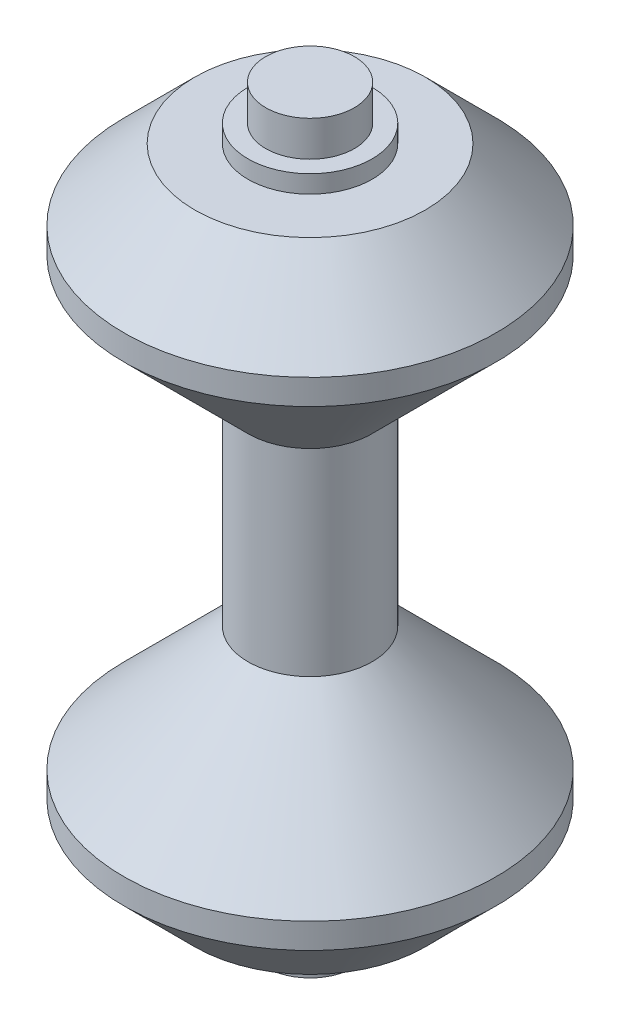
SolidWorks part; units mm, degrees
ref_plane "Front Plane" through (0, 0, 0) normal (0, 0, 1) x (1, 0, 0)
ref_plane "Top Plane" through (0, 0, 0) normal (0, 1, 0) x (1, 0, 0)
ref_plane "Right Plane" through (0, 0, 0) normal (1, 0, 0) x (0, 0, -1)
sketch "Sketch1" plane through (0, 0, 0) normal (0, 0, 1) x (1, 0, 0)
  line L0 (0, 21) -> (0, 0)
  line L1 (0, 21) -> (2.5, 21)
  line L2 (2.5, 21) -> (2.5, 19)
  line L3 (2.5, 19) -> (3.5, 19)
  line L4 (3.5, 19) -> (3.5, 18)
  line L5 (3.5, 18) -> (6.5, 18)
  line L6 (6.5, 18) -> (10.5, 14)
  line L7 (0, 0) -> (3.5, 0)
  line L8 (10.5, 14) -> (10.5, 12.5718)
  line L9 (10.5, 12.5718) -> (3.5, 5.5718)
  line L10 (3.5, 5.5718) -> (3.5, 0)
  circle A0 centre (19, 0) radius 14.9 construction
  point P2 (19, 0)
  dimension "D1" = 2.5
  dimension "D5" = 29.8
  dimension "D10" = 45
  dimension "D2" = 21
  dimension "D3" = 7
  dimension "D4" = 3.5
  dimension "D6" = 1
  dimension "D7" = 2
  dimension "D8" = 15.5
  dimension "D9" = 1
  dimension "D11" = 135
  dimension "D12" = 4
revolve "Revolve1" add sketch "Sketch1" angle 360 about L0
mirror "Mirror1" about plane through (0, 0, 0) normal (0, 1, 0) of "Revolve1"
